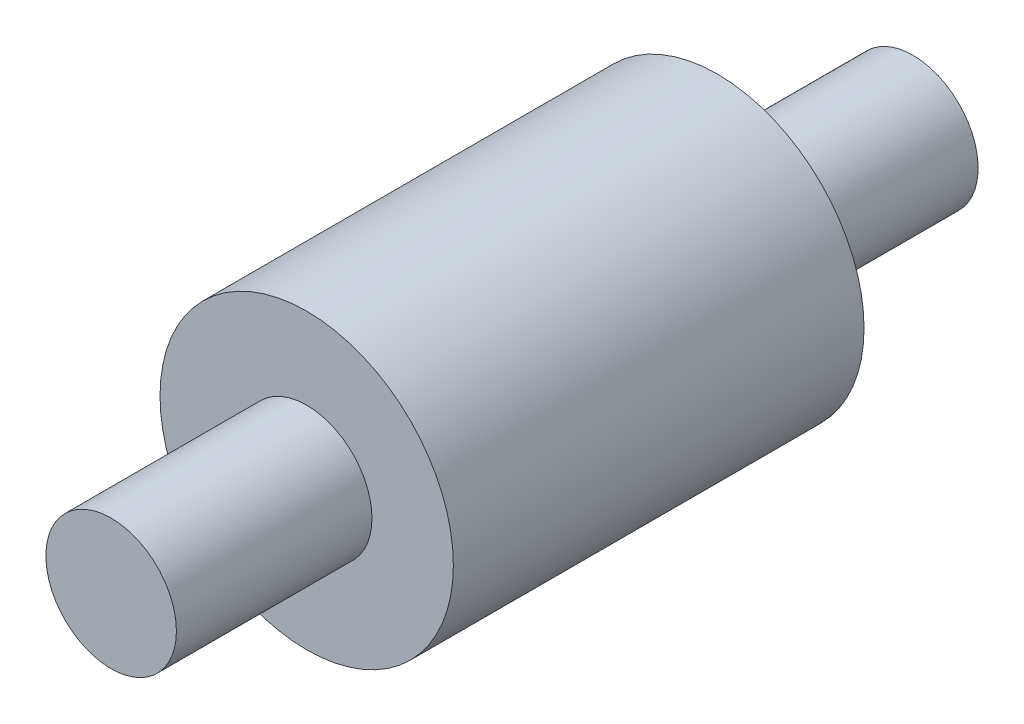
SolidWorks part; units mm, degrees
ref_plane "Front Plane" through (0, 0, 0) normal (0, 0, 1) x (1, 0, 0)
ref_plane "Top Plane" through (0, 0, 0) normal (0, 1, 0) x (1, 0, 0)
ref_plane "Right Plane" through (0, 0, 0) normal (1, 0, 0) x (0, 0, -1)
sketch "Sketch1" plane through (0, 0, 0) normal (0, 0, 1) x (1, 0, 0)
  circle A0 centre (0, 0) radius 2.25
  dimension "D1" = 4.5
extrude "Boss-Extrude1" add sketch "Sketch1" along normal blind 6.3
sketch "Sketch2" plane through (0, 0, 6.3) normal (0, 0, 1) x (1, 0, 0)
  circle A0 centre (0, 0) radius 1.0012
extrude "Boss-Extrude2" add sketch "Sketch2" along normal blind 3
sketch "Sketch3" plane through (0, 0, 0) normal (0, 0, -1) x (-1, 0, 0)
  circle A0 centre (0, 0) radius 1
  dimension "D1" = 2
extrude "Boss-Extrude3" add sketch "Sketch3" along normal blind 3
